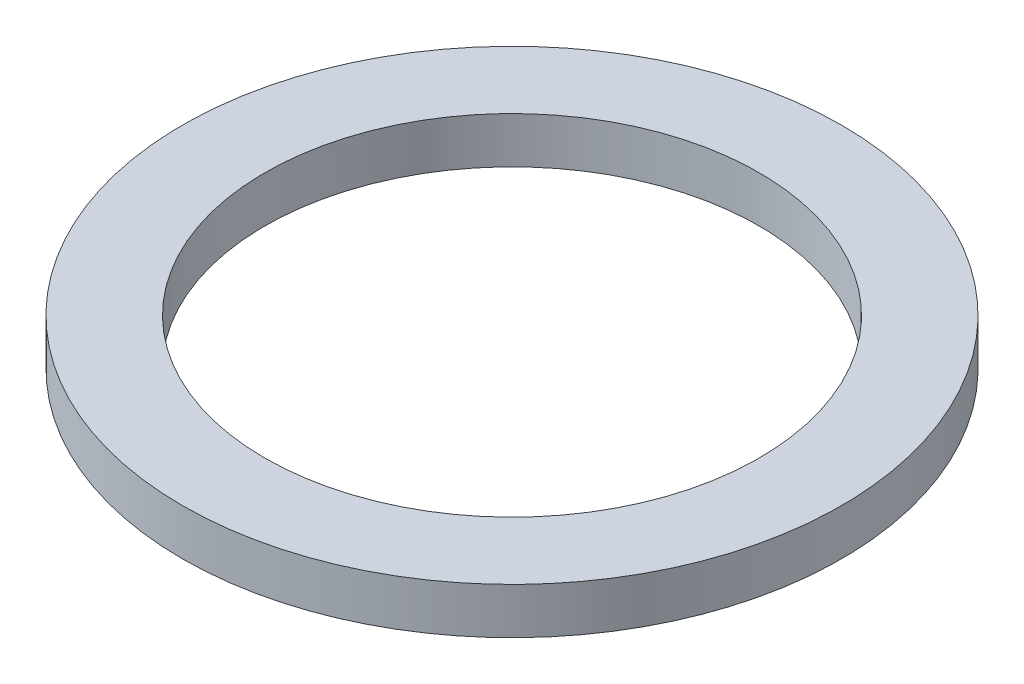
SolidWorks part; units mm, degrees
ref_plane "Front Plane" through (0, 0, 0) normal (0, 0, 1) x (1, 0, 0)
ref_plane "Top Plane" through (0, 0, 0) normal (0, 1, 0) x (1, 0, 0)
ref_plane "Right Plane" through (0, 0, 0) normal (1, 0, 0) x (0, 0, -1)
sketch "Sketch1" plane through (0, 0, 0) normal (0, 1, 0) x (1, 0, 0)
  circle A0 centre (0, 0) radius 6
  circle A1 centre (0, 0) radius 8
  dimension "D1" = 12
  dimension "D2" = 16
extrude "Boss-Extrude1" add sketch "Sketch1" along normal blind 1.12
